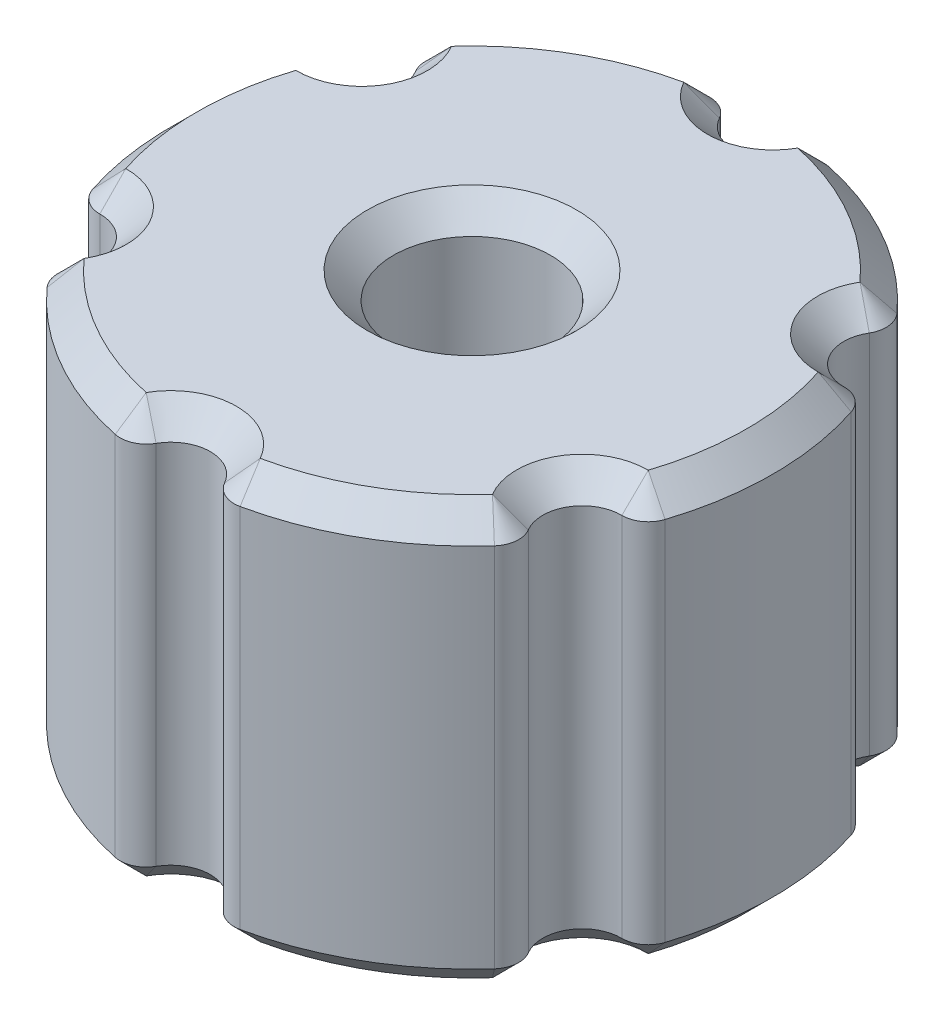
SolidWorks part; units mm, degrees
ref_plane "Plano frontal" through (0, 0, 0) normal (0, 0, 1) x (1, 0, 0)
ref_plane "Plano superior" through (0, 0, 0) normal (0, 1, 0) x (1, 0, 0)
ref_plane "Plano direito" through (0, 0, 0) normal (1, 0, 0) x (0, 0, -1)
sketch "Esboço1" plane through (0, 0, 0) normal (0, 1, 0) x (1, 0, 0)
  circle A0 centre (0, 0) radius 11.5
  circle A1 centre (0, 0) radius 3
  dimension "D1" = 23
  dimension "D2" = 6
extrude "Ressalto-extrusão1" add sketch "Esboço1" along normal blind 16
sketch "Esboço2" plane through (0, 16, 0) normal (0, 1, 0) x (1, 0, 0)
  circle A0 centre (0, 11.5034) radius 1.5034
  circle A1 centre (0, 0) radius 11.5 construction
  circle A2 centre (9.9623, 5.7517) radius 1.5034
  circle A3 centre (9.9623, -5.7517) radius 1.5034
  circle A4 centre (0, -11.5034) radius 1.5034
  circle A5 centre (-9.9623, -5.7517) radius 1.5034
  circle A6 centre (-9.9623, 5.7517) radius 1.5034
  point P2 (-1.5, 11.4018)
  point P7 (0, 10)
  point P11 (1.5, 11.4018)
  point P12 (0, 11.5)
  point P13 (9.1242, 6.9999)
  point P14 (8.6603, 5)
  point P15 (10.6242, 4.4018)
  point P16 (9.9593, 5.75)
  point P19 (10.6242, -4.4018)
  point P20 (8.6603, -5)
  point P21 (9.1242, -6.9999)
  point P22 (9.9593, -5.75)
  point P25 (1.5, -11.4018)
  point P26 (0, -10)
  point P27 (-1.5, -11.4018)
  point P28 (0, -11.5)
  point P31 (-9.1242, -6.9999)
  point P32 (-8.6603, -5)
  point P33 (-10.6242, -4.4018)
  point P34 (-9.9593, -5.75)
  point P37 (-10.6242, 4.4018)
  point P38 (-8.6603, 5)
  point P39 (-9.1242, 6.9999)
  point P40 (-9.9593, 5.75)
  point P41 (0.6019, -0.3475)
  point P42 (0, 0)
  dimension "D1" = 1.5
  dimension "D2" = 3
  dimension "D3" = 6
extrude "Corte-extrusão1" cut sketch "Esboço2" against normal through all both and the other way through all
fillet "Filete2" radius 1 12 edges at (-1.5, 8, -11.4018) (1.5, 8, -11.4018) (-10.6242, 8, -4.4018) (-9.1242, 8, -6.9999) (-9.1242, 8, 6.9999) (-10.6242, 8, 4.4018) (1.5, 8, 11.4018) (-1.5, 8, 11.4018) (10.6242, 8, 4.4018) (9.1242, 8, 6.9999) (9.1242, 8, -6.9999) (10.6242, 8, -4.4018)
chamfer "Chanfro1" distance 1 angle 45 50 edges at (0, 0, 3) (0, 16, 3) (0, 0, -10) (0, 16, -10) (5.75, 0, -9.9593) (1.7682, 0, -11.183) (-1.7682, 0, -11.183) (-5.75, 0, -9.9593) (-5.75, 16, -9.9593) (-1.7682, 16, -11.183) (1.7682, 16, -11.183) (5.75, 16, -9.9593) (-8.6603, 0, -5) (-8.6603, 0, 5) (0, 0, 10) (8.6603, 0, 5) (8.6603, 0, -5) (8.6603, 16, -5) (8.6603, 16, 5) (0, 16, 10) (-8.6603, 16, 5) (-8.6603, 16, -5) (-8.8006, 0, -7.1228) (-10.5689, 0, -4.0602) (-11.5, 0, 0) (-10.5689, 0, 4.0602) (-8.8006, 0, 7.1228) (-5.75, 0, 9.9593) (-1.7682, 0, 11.183) (1.7682, 0, 11.183) (5.75, 0, 9.9593) (8.8006, 0, 7.1228) (10.5689, 0, 4.0602) (11.5, 0, 0) (10.5689, 0, -4.0602) (8.8006, 0, -7.1228) (8.8006, 16, -7.1228) (10.5689, 16, -4.0602) (11.5, 16, 0) (10.5689, 16, 4.0602) (8.8006, 16, 7.1228) (5.75, 16, 9.9593) (1.7682, 16, 11.183) (-1.7682, 16, 11.183) (-5.75, 16, 9.9593) (-8.8006, 16, 7.1228) (-10.5689, 16, 4.0602) (-11.5, 16, 0) (-10.5689, 16, -4.0602) (-8.8006, 16, -7.1228)
